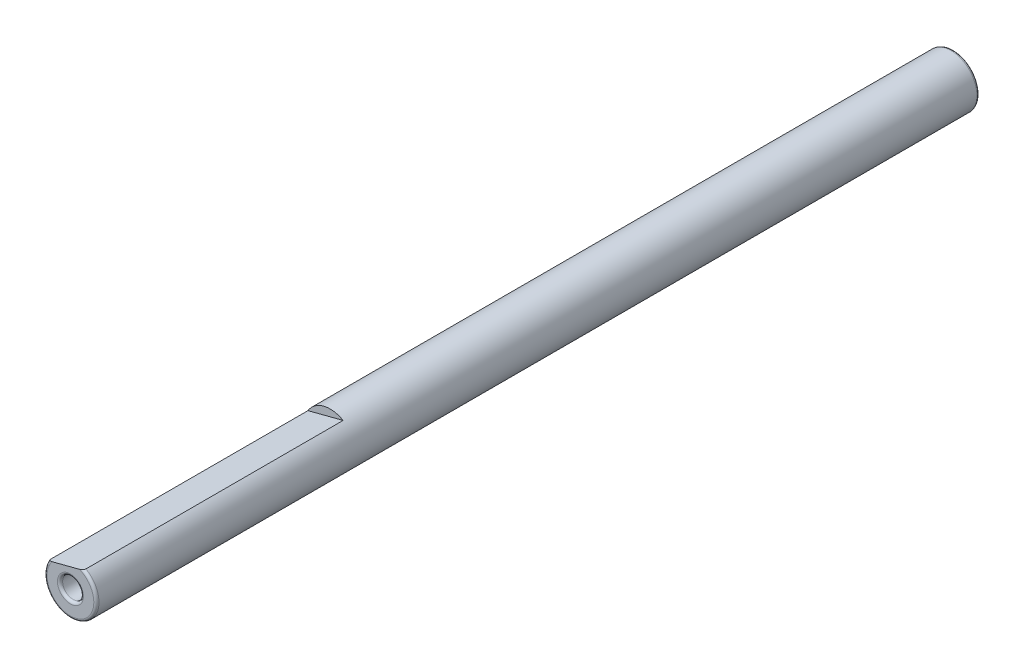
SolidWorks part; units mm, degrees
material "Acero aleado"
ref_plane "Alzado" through (0, 0, 0) normal (0, 0, 1) x (1, 0, 0)
ref_plane "Planta" through (0, 0, 0) normal (0, 1, 0) x (1, 0, 0)
ref_plane "Vista lateral" through (0, 0, 0) normal (1, 0, 0) x (0, 0, -1)
sketch "Croquis1" plane through (0, 0, 0) normal (0, 0, 1) x (1, 0, 0)
  circle A0 centre (0, 0) radius 2.5
  dimension "D1" = 5
extrude "Saliente-Extruir1" add sketch "Croquis1" along normal blind 85
sketch "Croquis2" plane through (0, 0, 85) normal (0, 0, 1) x (1, 0, 0)
  circle A0 centre (0, 0) radius 1
  dimension "D1" = 2
extrude "Cortar-Extruir1" cut sketch "Croquis2" against normal through all
fillet "Redondeo1" radius 0.25 3 edges at (2.5, 0, 85) (1, 0, 85) (2.5, 0, 0)
sketch "Esquisse1" plane through (0, 0, 85) normal (0, 0, 1) x (1, 0, 0)
  line L0 (-2.1417, 1.2897) -> (1.2466, 2.167)
  arc A0 (1.2466, 2.167) -> (-2.1417, 1.2897) centre (0, 0) ccw
  circle A1 centre (0, 0) radius 2.5 construction
  circle A2 centre (0, 0) radius 2.5 construction
  dimension "D1" = 3.5
extrude "Enlèv. mat.-Extru.1" cut sketch "Esquisse1" against normal blind 25
